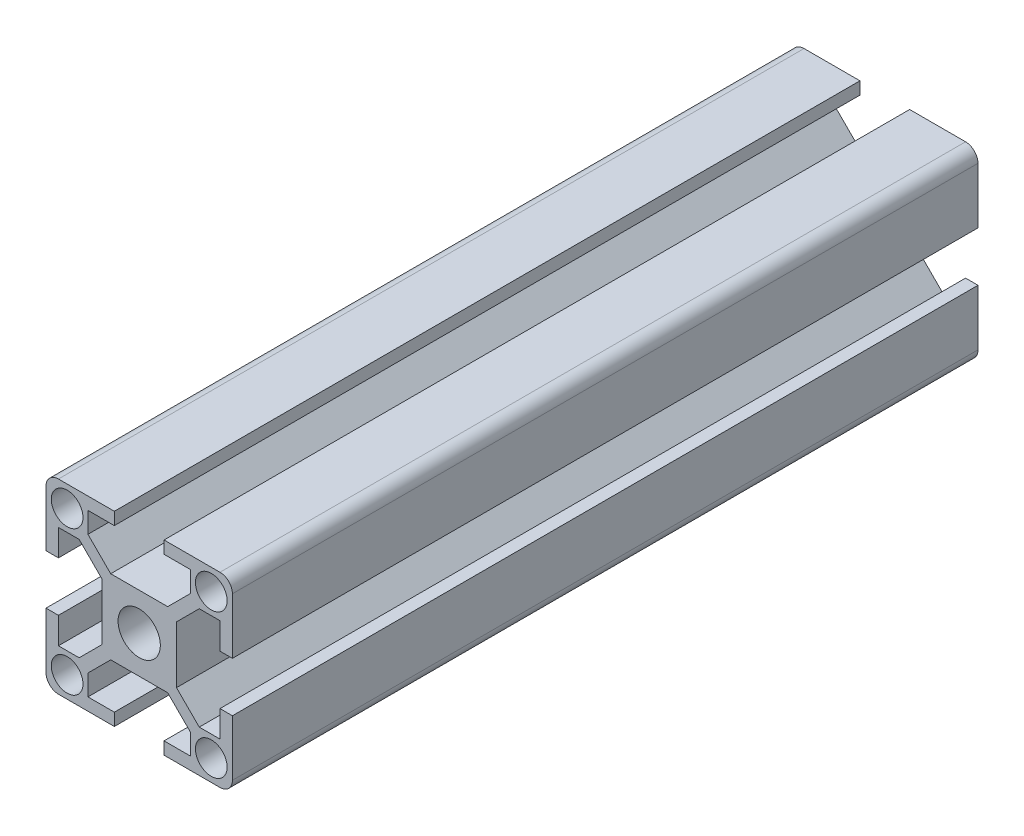
SolidWorks part; units mm, degrees
ref_plane "Front Plane" through (0, 0, 0) normal (0, 0, 1) x (1, 0, 0)
ref_plane "Top Plane" through (0, 0, 0) normal (0, 1, 0) x (1, 0, 0)
ref_plane "Right Plane" through (0, 0, 0) normal (1, 0, 0) x (0, 0, -1)
ref_plane "Plane1" through (0, 6.25, 0) normal (0, -1, 0) x (1, 0, 0)
sketch "Sketch1" plane through (0, 0, 0) normal (0, 0, 1) x (1, 0, 0)
  line L0 (-13, -15) -> (-4, -15)
  line L1 (-4, -15) -> (-4, -13)
  line L2 (-4, -13) -> (-8.25, -13)
  line L3 (-8.25, -13) -> (-8.25, -9.6642)
  line L4 (-8.25, -9.6642) -> (-4.5858, -6)
  line L5 (-4.5858, -6) -> (4.5858, -6)
  line L6 (4.5858, -6) -> (8.25, -9.6642)
  line L7 (8.25, -9.6642) -> (8.25, -13)
  line L8 (8.25, -13) -> (4, -13)
  line L9 (4, -13) -> (4, -15)
  line L10 (4, -15) -> (13, -15)
  line L11 (15, -13) -> (15, -4)
  line L12 (15, -4) -> (13, -4)
  line L13 (13, -4) -> (13, -8.25)
  line L14 (13, -8.25) -> (9.6642, -8.25)
  line L15 (9.6642, -8.25) -> (6, -4.5858)
  line L16 (6, -4.5858) -> (6, 4.5858)
  line L17 (6, 4.5858) -> (9.6642, 8.25)
  line L18 (9.6642, 8.25) -> (13, 8.25)
  line L19 (13, 8.25) -> (13, 4)
  line L20 (13, 4) -> (15, 4)
  line L21 (15, 4) -> (15, 13)
  line L22 (13, 15) -> (4, 15)
  line L23 (4, 15) -> (4, 13)
  line L24 (4, 13) -> (8.25, 13)
  line L25 (8.25, 13) -> (8.25, 9.6642)
  line L26 (8.25, 9.6642) -> (4.5858, 6)
  line L27 (4.5858, 6) -> (-4.5858, 6)
  line L28 (-4.5858, 6) -> (-8.25, 9.6642)
  line L29 (-8.25, 9.6642) -> (-8.25, 13)
  line L30 (-8.25, 13) -> (-4, 13)
  line L31 (-4, 13) -> (-4, 15)
  line L32 (-4, 15) -> (-13, 15)
  line L33 (-15, 13) -> (-15, 4)
  line L34 (-15, 4) -> (-13, 4)
  line L35 (-13, 4) -> (-13, 8.25)
  line L36 (-13, 8.25) -> (-9.6642, 8.25)
  line L37 (-9.6642, 8.25) -> (-6, 4.5858)
  line L38 (-6, 4.5858) -> (-6, -4.5858)
  line L39 (-6, -4.5858) -> (-9.6642, -8.25)
  line L40 (-9.6642, -8.25) -> (-13, -8.25)
  line L41 (-13, -8.25) -> (-13, -4)
  line L42 (-13, -4) -> (-15, -4)
  line L43 (-15, -4) -> (-15, -13)
  circle A0 centre (-11.6, 11.6) radius 2.55
  circle A1 centre (0, 0) radius 3.4
  circle A2 centre (-11.6, -11.6) radius 2.55
  circle A3 centre (11.6, -11.6) radius 2.55
  circle A4 centre (11.6, 11.6) radius 2.55
  arc A5 (-13, -15) -> (-15, -13) centre (-13, -13) cw
  arc A6 (15, -13) -> (13, -15) centre (13, -13) cw
  arc A7 (13, 15) -> (15, 13) centre (13, 13) cw
  arc A8 (-15, 13) -> (-13, 15) centre (-13, 13) cw
  dimension "D1" = 5.1
  dimension "D2" = 6.8
  dimension "D3" = 2
  dimension "D8" = 2
  dimension "D9" = 2
  dimension "D10" = 4
  dimension "D4" = 11.6
  dimension "D5" = 11.6
  dimension "D6" = 11.6
  dimension "D7" = 11.6
  dimension "D11" = 6
  dimension "D12" = 4.5858
  dimension "D13" = 4.5858
  dimension "D14" = 8.25
  dimension "D15" = 15
  dimension "D16" = 4
  dimension "D17" = 6
  dimension "D18" = 9.6642
  dimension "D19" = 9.6642
  dimension "D20" = 4
  dimension "D21" = 4.5858
  dimension "D22" = 6
  dimension "D23" = 8.25
  dimension "D24" = 4.5858
  dimension "D25" = 4.5858
  dimension "D26" = 9.6642
  dimension "D27" = 15
  dimension "D30" = 9.6642
  dimension "D31" = 9.6642
extrude "Boss-Extrude1" add sketch "Sketch1" along normal blind 120
